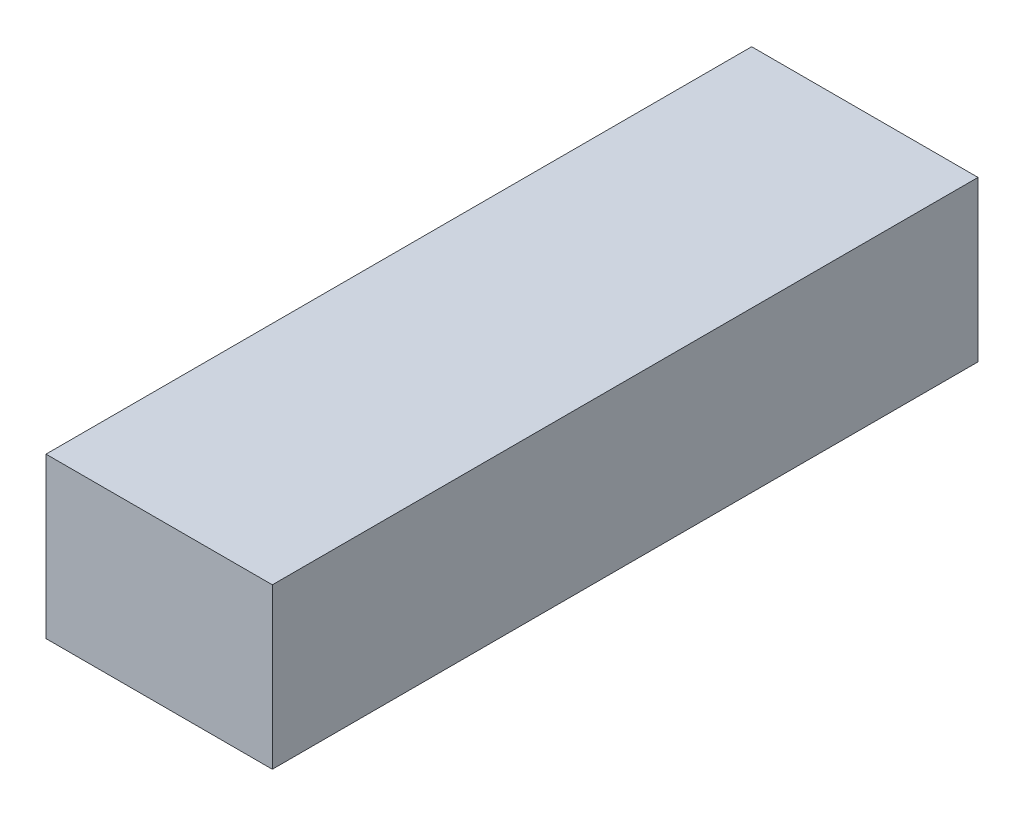
SolidWorks part; units mm, degrees
ref_plane "Front Plane" through (0, 0, 0) normal (0, 0, 1) x (1, 0, 0)
ref_plane "Top Plane" through (0, 0, 0) normal (0, 1, 0) x (1, 0, 0)
ref_plane "Right Plane" through (0, 0, 0) normal (1, 0, 0) x (0, 0, -1)
sketch "Sketch1" plane through (0, 0, 0) normal (0, 1, 0) x (1, 0, 0)
  line L1 (-17, -53) -> (17, -53)
  line L2 (-17, -53) -> (-17, 53)
  line L3 (-17, 53) -> (17, 53)
  line L4 (17, -53) -> (17, 53)
  line L5 (-17, -53) -> (17, 53) construction
  line L6 (-17, 53) -> (17, -53) construction
  point P0 (0, 0)
extrude "Boss-Extrude1" add sketch "Sketch1" along normal blind 24
